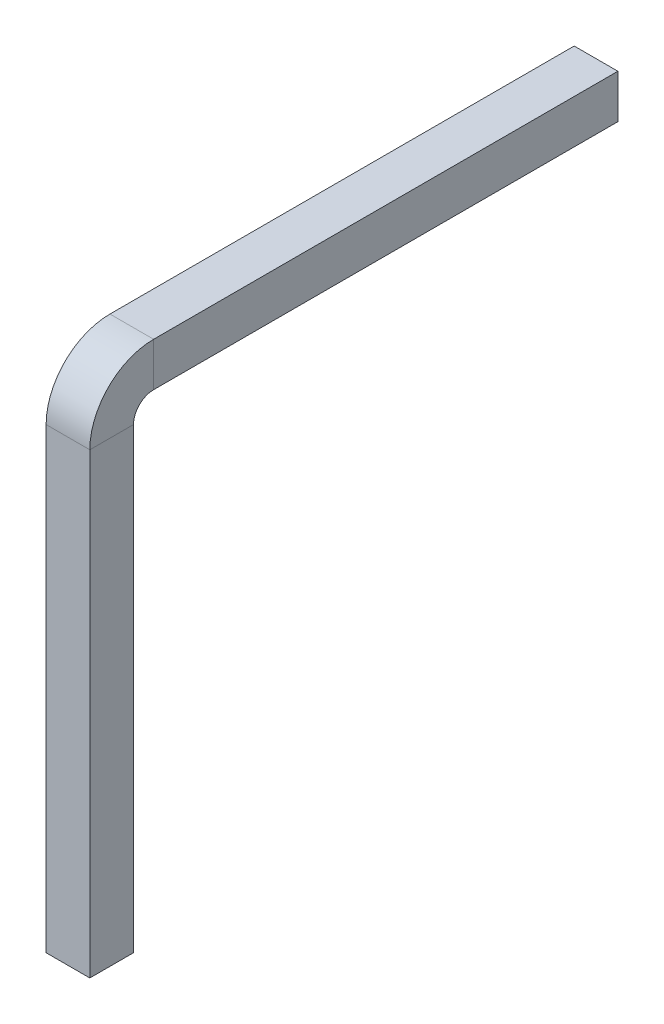
SolidWorks part; units mm, degrees
material "Brass"
ref_plane "Front Plane" through (0, 0, 0) normal (0, 0, 1) x (1, 0, 0)
ref_plane "Top Plane" through (0, 0, 0) normal (0, 1, 0) x (1, 0, 0)
ref_plane "Right Plane" through (0, 0, 0) normal (1, 0, 0) x (0, 0, -1)
sketch "Sketch1" plane through (0, 0, 0) normal (0, 1, 0) x (1, 0, 0)
  line L1 (0.32, 0.32) -> (-0.32, 0.32)
  line L2 (0.32, 0.32) -> (0.32, -0.32)
  line L3 (0.32, -0.32) -> (-0.32, -0.32)
  line L4 (-0.32, 0.32) -> (-0.32, -0.32)
  line L5 (0.32, 0.32) -> (-0.32, -0.32) construction
  line L6 (0.32, -0.32) -> (-0.32, 0.32) construction
  point P0 (0, 0)
  dimension "D1" = 0.64
sketch "Sketch2" plane through (0, 0, 0) normal (1, 0, 0) x (0, 0, -1)
  line L0 (0.0147, 0) -> (0.0147, 6.9)
  line L1 (-0.32, 0) -> (0.32, 0) construction
  line L2 (0.6147, 7.5) -> (7.6147, 7.5)
  arc A0 (0.0147, 6.9) -> (0.6147, 7.5) centre (0.6147, 6.9) cw
  dimension "D1" = 0.6
sweep "Sweep1" add profiles "Sketch1" path "Sketch2"
chamfer "Chamfer1" distance 0.2 angle 45 8 edges at (0, 7.1947, -7.6147) (0.32, 7.5147, -7.6147) (0, 7.8347, -7.6147) (-0.32, 7.5147, -7.6147) (0, 0, 0.32) (0.32, 0, 0) (0, 0, -0.32) (-0.32, 0, 0)
